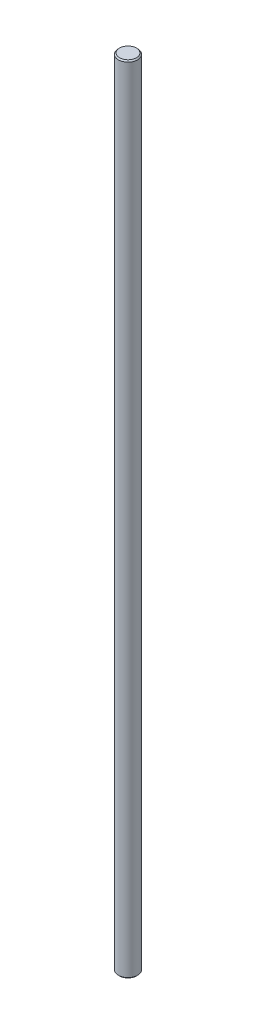
SolidWorks part; units mm, degrees
ref_plane "Front Plane" through (0, 0, 0) normal (0, 0, 1) x (1, 0, 0)
ref_plane "Top Plane" through (0, 0, 0) normal (0, 1, 0) x (1, 0, 0)
ref_plane "Right Plane" through (0, 0, 0) normal (1, 0, 0) x (0, 0, -1)
sketch "Sketch1" plane through (0, 0, 0) normal (0, 1, 0) x (1, 0, 0)
  circle A0 centre (0, 0) radius 4
  dimension "D1" = 8
extrude "Boss-Extrude1" add sketch "Sketch1" along normal mid plane 330
chamfer "Chamfer1" distance 0.5 angle 45 2 edges at (0, -165, 4) (0, 165, 4)
